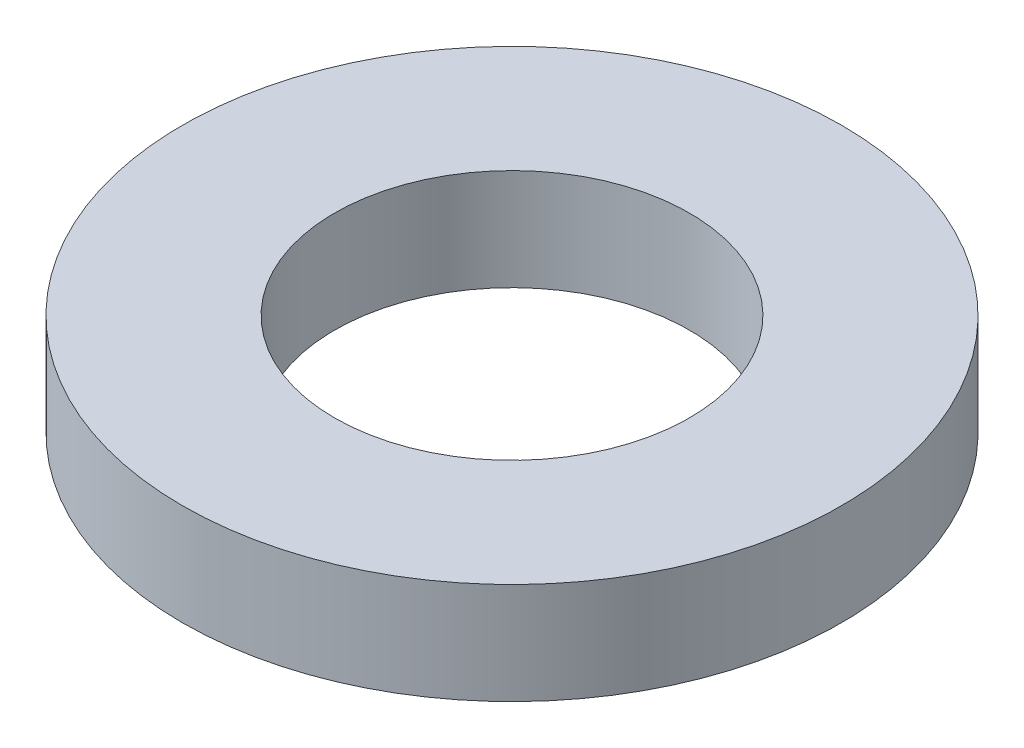
SolidWorks part; units mm, degrees
ref_plane "Ebene vorne" through (0, 0, 0) normal (0, 0, 1) x (1, 0, 0)
ref_plane "Ebene oben" through (0, 0, 0) normal (0, 1, 0) x (1, 0, 0)
ref_plane "Ebene rechts" through (0, 0, 0) normal (1, 0, 0) x (0, 0, -1)
sketch "Skizze1" plane through (0, 0, 0) normal (0, 1, 0) x (1, 0, 0)
  circle A0 centre (0, 0) radius 3.25
  circle A1 centre (0, 0) radius 1.75
  dimension "D1" = 3.5
  dimension "D2" = 1.5
extrude "Aufsatz-Linear austragen1" add sketch "Skizze1" along normal blind 1
